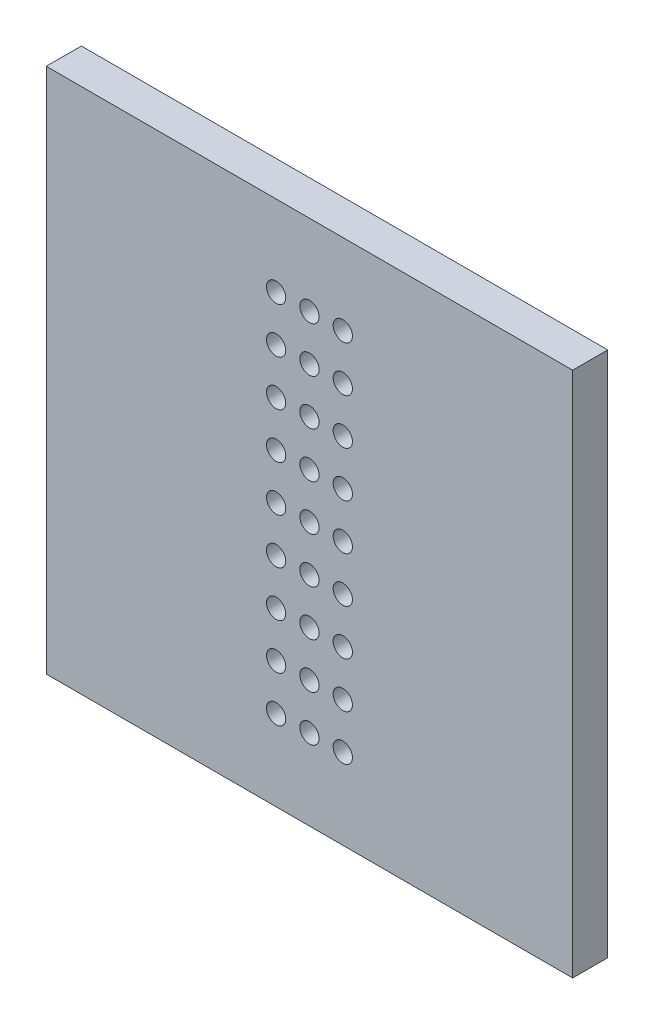
SolidWorks part; units mm, degrees
ref_plane "Plan de face" through (0, 0, 0) normal (0, 0, 1) x (1, 0, 0)
ref_plane "Plan de dessus" through (0, 0, 0) normal (0, 1, 0) x (1, 0, 0)
ref_plane "Plan de droite" through (0, 0, 0) normal (1, 0, 0) x (0, 0, -1)
sketch "Esquisse1" plane through (0, 0, 0) normal (0, 0, 1) x (1, 0, 0)
  line L1 (-15, -15) -> (15, -15)
  line L2 (-15, -15) -> (-15, 15)
  line L3 (-15, 15) -> (15, 15)
  line L4 (15, -15) -> (15, 15)
  line L5 (-15, -15) -> (15, 15) construction
  line L6 (-15, 15) -> (15, -15) construction
  point P0 (0, 0)
extrude "Base_Plate" add sketch "Esquisse1" along normal blind 2
sketch "Sketch_Perforations" plane through (0, 0, 2) normal (0, 0, 1) x (1, 0, 0)
  circle A0 centre (-1.9, -10.4) radius 0.55
  circle A1 centre (-1.9, -7.8) radius 0.55
  circle A2 centre (-1.9, -5.2) radius 0.55
  circle A3 centre (-1.9, -2.6) radius 0.55
  circle A4 centre (-1.9, 0) radius 0.55
  circle A5 centre (-1.9, 2.6) radius 0.55
  circle A6 centre (-1.9, 5.2) radius 0.55
  circle A7 centre (-1.9, 7.8) radius 0.55
  circle A8 centre (-1.9, 10.4) radius 0.55
  circle A9 centre (0, -10.4) radius 0.55
  circle A10 centre (0, -7.8) radius 0.55
  circle A11 centre (0, -5.2) radius 0.55
  circle A12 centre (0, -2.6) radius 0.55
  circle A13 centre (0, 0) radius 0.55
  circle A14 centre (0, 2.6) radius 0.55
  circle A15 centre (0, 5.2) radius 0.55
  circle A16 centre (0, 7.8) radius 0.55
  circle A17 centre (0, 10.4) radius 0.55
  circle A18 centre (1.9, -10.4) radius 0.55
  circle A19 centre (1.9, -7.8) radius 0.55
  circle A20 centre (1.9, -5.2) radius 0.55
  circle A21 centre (1.9, -2.6) radius 0.55
  circle A22 centre (1.9, 0) radius 0.55
  circle A23 centre (1.9, 2.6) radius 0.55
  circle A24 centre (1.9, 5.2) radius 0.55
  circle A25 centre (1.9, 7.8) radius 0.55
  circle A26 centre (1.9, 10.4) radius 0.55
extrude "Cut_Perforations" cut sketch "Sketch_Perforations" against normal blind 10
